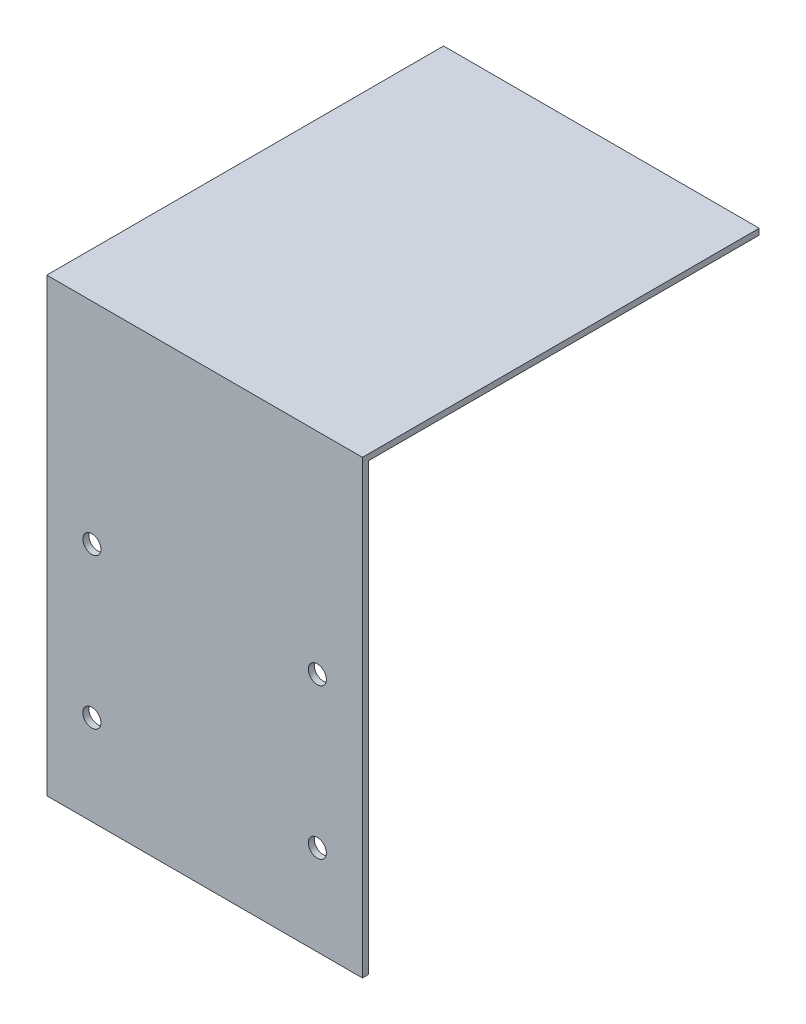
SolidWorks part; units mm, degrees
ref_plane "Front Plane" through (0, 0, 0) normal (0, 0, 1) x (1, 0, 0)
ref_plane "Top Plane" through (0, 0, 0) normal (0, 1, 0) x (1, 0, 0)
ref_plane "Right Plane" through (0, 0, 0) normal (1, 0, 0) x (0, 0, -1)
sketch "Sketch1" plane through (0, 0, 0) normal (0, 0, 1) x (1, 0, 0)
  line L0 (0, 0) -> (0, 150)
  line L1 (0, 0) -> (105, 0)
  line L2 (105, 0) -> (105, 150)
  line L3 (105, 150) -> (0, 150)
  line L4 (0, 150) -> (0, 149.2368)
  dimension "D1" = 150
  dimension "D2" = 105
extrude "Boss-Extrude1" add sketch "Sketch1" along normal blind 2 contours L0 L1 L2 L3
sketch "Sketch2" plane through (0, 0, 0) normal (0, 0, -1) x (-1, 0, 0)
  line L0 (-105, 150) -> (0, 150)
  line L1 (0, 150) -> (0, 148)
  line L2 (0, 0) -> (0, 150) construction
  line L3 (0, 148) -> (-105, 148)
  line L4 (-105, 0) -> (-105, 150) construction
  line L5 (-105, 148) -> (-105, 150)
  dimension "D1" = 2
extrude "Boss-Extrude2" add sketch "Sketch2" along normal blind 130
sketch "Sketch3" plane through (0, 0, 2) normal (0, 0, 1) x (1, 0, 0)
  line L0 (0, 0) -> (0, 30) construction
  line L1 (0, 0) -> (0, 150) construction
  line L2 (0, 30) -> (15, 30) construction
  circle A0 centre (15, 30) radius 3
  dimension "D1" = 30
  dimension "D2" = 15
extrude "Cut-Extrude1" cut sketch "Sketch3" against normal blind 10
sketch "Sketch4" plane through (0, 0, 2) normal (0, 0, 1) x (1, 0, 0)
  line L0 (105, 0) -> (105, 30) construction
  line L1 (105, 0) -> (105, 150) construction
  line L2 (105, 30) -> (90, 30) construction
  circle A0 centre (90, 30) radius 3
  dimension "D1" = 30
  dimension "D2" = 15
extrude "Cut-Extrude2" cut sketch "Sketch4" against normal blind 10
sketch "Sketch5" plane through (0, 0, 2) normal (0, 0, 1) x (1, 0, 0)
  line L0 (0, 0) -> (0, 80)
  line L1 (0, 0) -> (0, 150) construction
  line L2 (0, 80) -> (15, 80) construction
  circle A0 centre (15, 80) radius 3
  dimension "D1" = 80
  dimension "D2" = 15
extrude "Cut-Extrude3" cut sketch "Sketch5" against normal blind 10 contours A0
sketch "Sketch6" plane through (0, 0, 2) normal (0, 0, 1) x (1, 0, 0)
  line L0 (105, 0) -> (105, 80) construction
  line L1 (105, 0) -> (105, 150) construction
  line L2 (105, 80) -> (90, 80)
  circle A0 centre (90, 80) radius 3
  dimension "D1" = 80
  dimension "D2" = 15
extrude "Cut-Extrude4" cut sketch "Sketch6" against normal blind 10 contours A0
